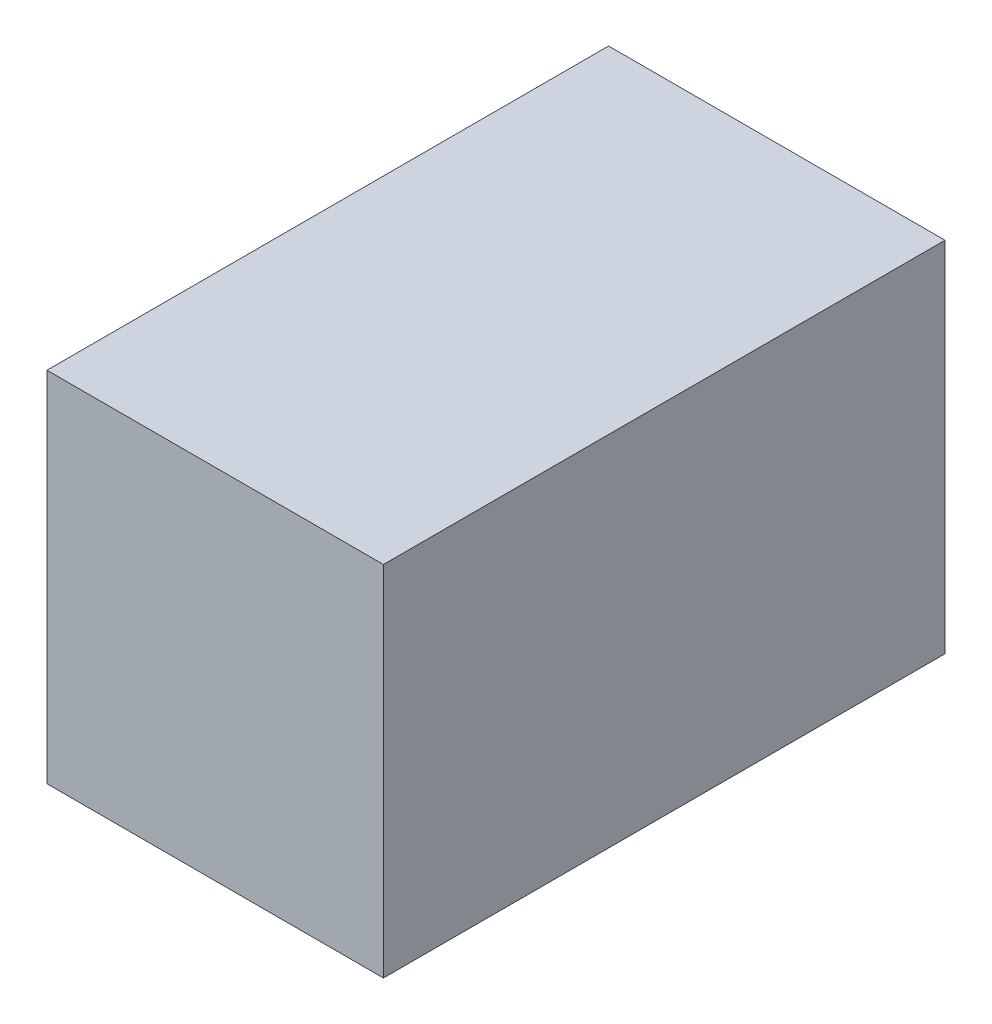
SolidWorks part; units mm, degrees
ref_plane "Front Plane" through (0, 0, 0) normal (0, 0, 1) x (1, 0, 0)
ref_plane "Top Plane" through (0, 0, 0) normal (0, 1, 0) x (1, 0, 0)
ref_plane "Right Plane" through (0, 0, 0) normal (1, 0, 0) x (0, 0, -1)
sketch "Sketch4" plane through (0, 0, 0) normal (1, 0, 0) x (0, 0, -1)
  line L1 (-15.525, 9.175) -> (15.525, 9.175)
  line L2 (-15.525, 9.175) -> (-15.525, -9.175)
  line L3 (-15.525, -9.175) -> (15.525, -9.175)
  line L4 (15.525, 9.175) -> (15.525, -9.175)
  line L5 (-15.525, 9.175) -> (15.525, -9.175) construction
  line L6 (-15.525, -9.175) -> (15.525, 9.175) construction
  point P0 (0, 0)
  dimension "D1" = 31.05
  dimension "D2" = 18.35
extrude "Boss-Extrude1" add sketch "Sketch4" along normal blind 19
shell "Shell1" thickness 2
sketch "Sketch5" plane through (0, 0, -17.525) normal (0, 0, -1) x (-1, 0, 0)
  line L0 (0, -11.175) -> (0, 11.175) construction
  line L1 (0, 9.175) -> (-12, 9.175)
  line L2 (-12, 9.175) -> (-12, -9.175)
  line L3 (-12, -9.175) -> (0, -9.175)
  line L4 (-21, 11.175) -> (0, 11.175) construction
  line L5 (-21, -11.175) -> (0, -11.175) construction
  line L6 (0, 9.175) -> (0, -9.175)
  dimension "D1" = 12
  dimension "D2" = 2
  dimension "D3" = 2
extrude "Cut-Extrude1" cut sketch "Sketch5" against normal up to surface (2 mm away) up to face at (9.5, 0, -15.525)
equation "\"terminalRad\"= 3mm"
equation "\"terminalLen\"= 10.5mm"
equation "\"threadlen\"=11"
